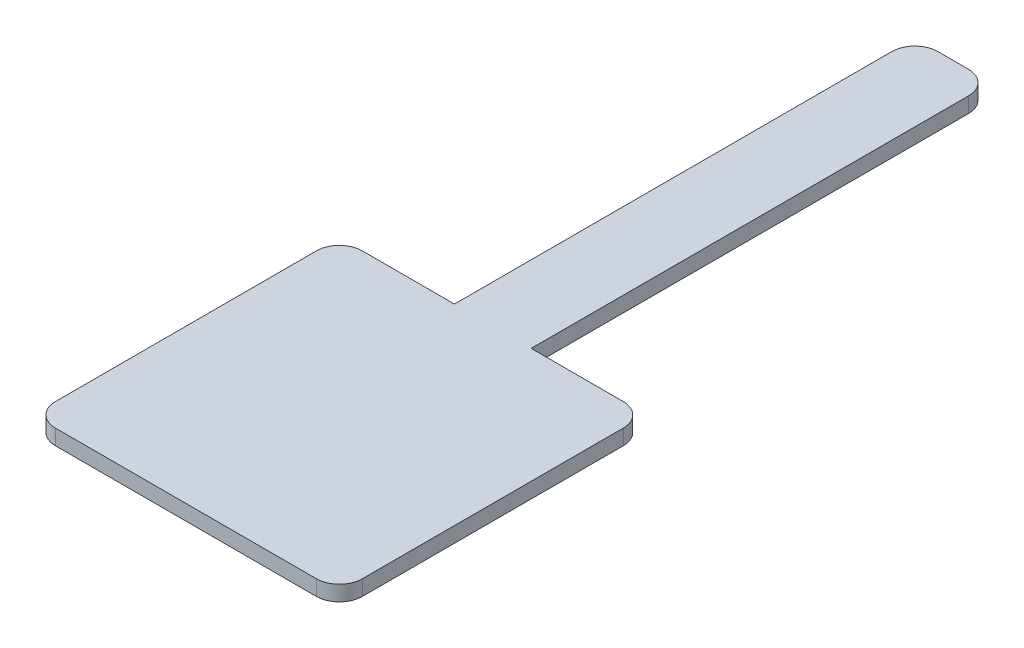
SolidWorks part; units mm, degrees
ref_plane "前视基准面" through (0, 0, 0) normal (0, 0, 1) x (1, 0, 0)
ref_plane "上视基准面" through (0, 0, 0) normal (0, 1, 0) x (1, 0, 0)
ref_plane "右视基准面" through (0, 0, 0) normal (1, 0, 0) x (0, 0, -1)
sketch "草图1" plane through (0, 0, 0) normal (0, 1, 0) x (1, 0, 0)
  line L0 (-24.804, -20.7201) -> (-4.804, -20.7201)
  line L1 (-4.804, -20.7201) -> (-4.804, -0.7201)
  line L2 (-4.804, -0.7201) -> (-12.304, -0.7201)
  line L3 (-12.304, -0.7201) -> (-12.304, 29.2799)
  line L4 (-12.304, 29.2799) -> (-17.304, 29.2799)
  line L5 (-17.304, 29.2799) -> (-17.304, -0.7201)
  line L6 (-17.304, -0.7201) -> (-24.804, -0.7201)
  line L7 (-24.804, -0.7201) -> (-24.804, -20.7201)
extrude "凸台-拉伸1" add sketch "草图1" along normal blind 1
fillet "圆角1" radius 1.5 6 edges at (-17.304, 0.5, -29.2799) (-12.304, 0.5, -29.2799) (-24.804, 0.5, 0.7201) (-4.804, 0.5, 0.7201) (-4.804, 0.5, 20.7201) (-24.804, 0.5, 20.7201)
